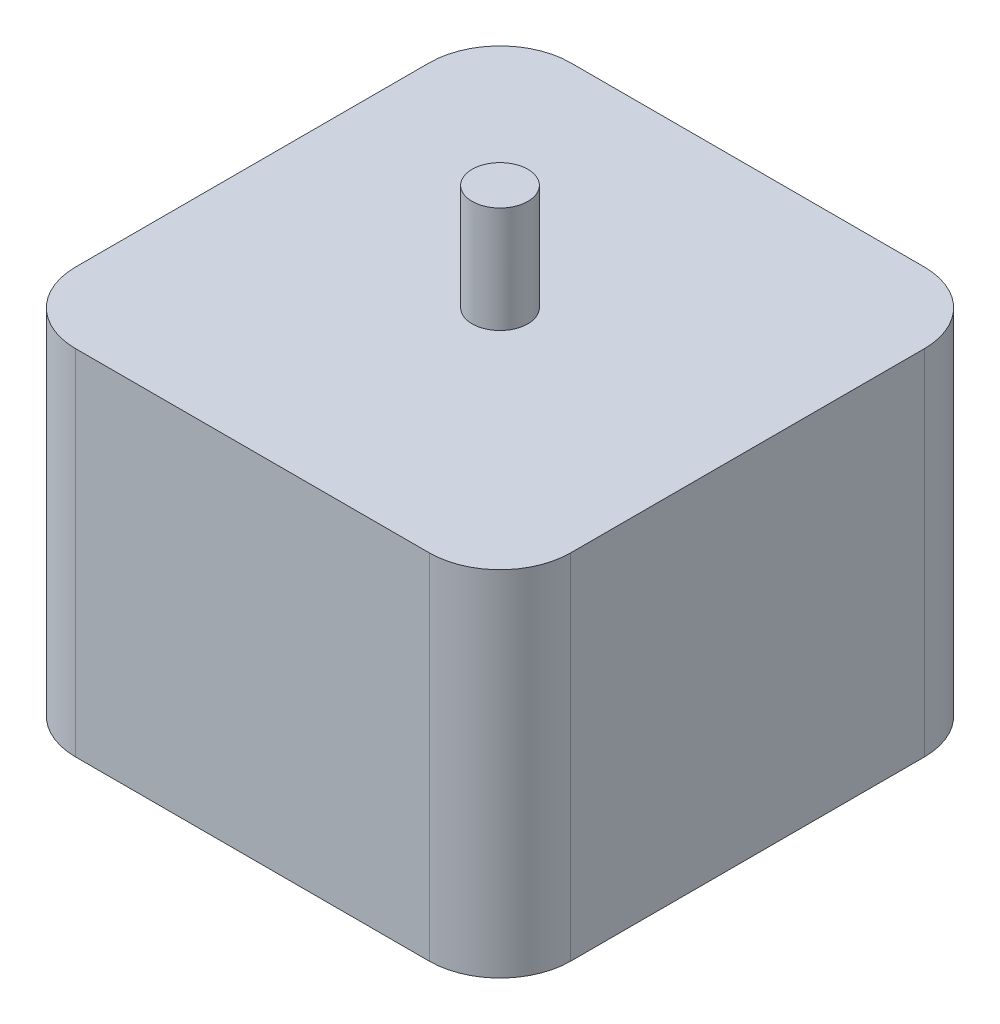
SolidWorks part; units mm, degrees
ref_plane "Front Plane" through (0, 0, 0) normal (0, 0, 1) x (1, 0, 0)
ref_plane "Top Plane" through (0, 0, 0) normal (0, 1, 0) x (1, 0, 0)
ref_plane "Right Plane" through (0, 0, 0) normal (1, 0, 0) x (0, 0, -1)
sketch "Sketch1" plane through (0, 0, 0) normal (0, 1, 0) x (1, 0, 0)
  line L1 (-22.225, -22.225) -> (22.225, -22.225)
  line L2 (-22.225, -22.225) -> (-22.225, 22.225)
  line L3 (-22.225, 22.225) -> (22.225, 22.225)
  line L4 (22.225, -22.225) -> (22.225, 22.225)
  line L5 (-22.225, -22.225) -> (22.225, 22.225) construction
  line L6 (-22.225, 22.225) -> (22.225, -22.225) construction
  point P0 (0, 0)
  dimension "D1" = 44.45
  dimension "D2" = 44.45
extrude "Boss-Extrude1" add sketch "Sketch1" along normal blind 31.75
fillet "Fillet1" radius 6.35 4 edges at (-22.225, 15.875, -22.225) (-22.225, 15.875, 22.225) (22.225, 15.875, -22.225) (22.225, 15.875, 22.225)
sketch "Sketch2" plane through (0, 31.75, 0) normal (0, 1, 0) x (1, 0, 0)
  circle A0 centre (0, 0) radius 2.5
  dimension "D1" = 5
extrude "Boss-Extrude2" add sketch "Sketch2" along normal blind 9.525
sketch "Sketch4" plane through (0, 0, 0) normal (0, -1, 0) x (1, 0, 0)
  circle A0 centre (0, 0) radius 2.5
  dimension "D1" = 5
extrude "Boss-Extrude3" add sketch "Sketch4" along normal blind 9.525
